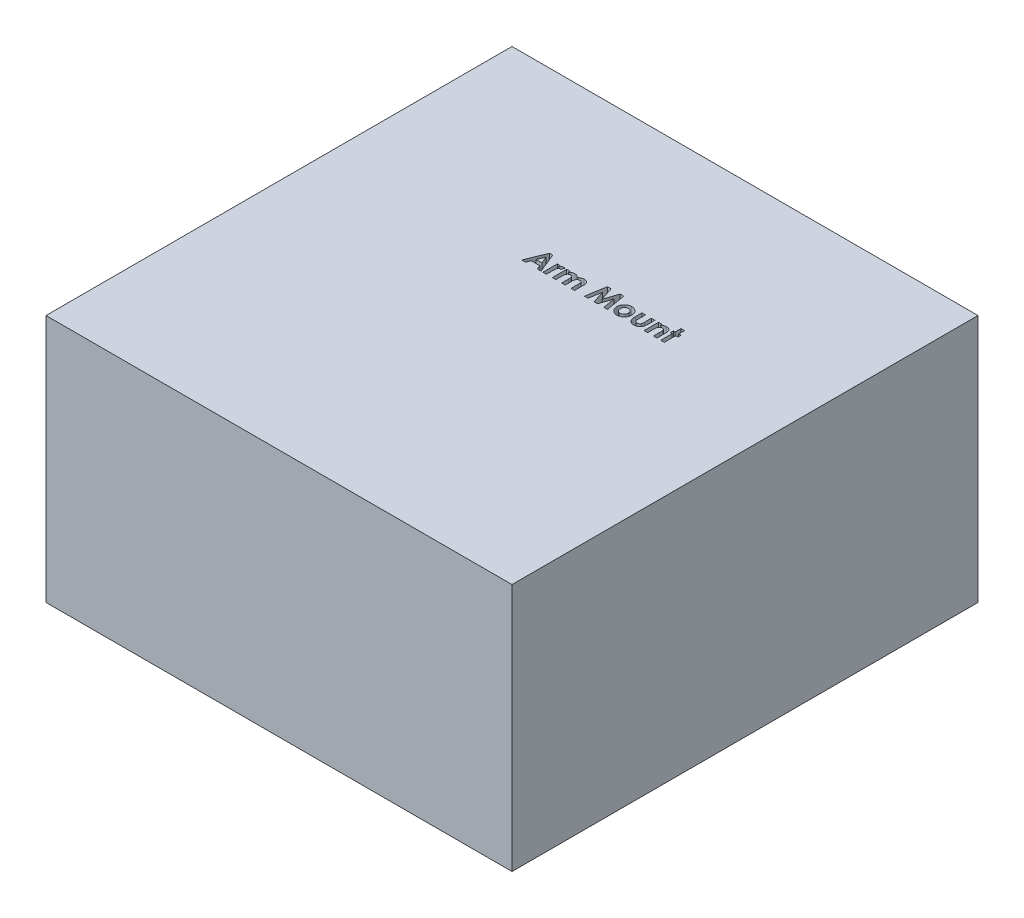
SolidWorks part; units mm, degrees
ref_plane "Front Plane" through (0, 0, 0) normal (0, 0, 1) x (1, 0, 0)
ref_plane "Top Plane" through (0, 0, 0) normal (0, 1, 0) x (1, 0, 0)
ref_plane "Right Plane" through (0, 0, 0) normal (1, 0, 0) x (0, 0, -1)
sketch "Sketch1" plane through (0, 0, 0) normal (0, 1, 0) x (1, 0, 0)
  line L1 (0, 0) -> (300, 0)
  line L2 (0, 0) -> (0, 300)
  line L3 (0, 300) -> (300, 300)
  line L4 (300, 0) -> (300, 300)
  dimension "D1" = 300
  dimension "D2" = 300
extrude "Boss-Extrude1" add sketch "Sketch1" along normal blind 160
sketch "Sketch2" plane through (0, 160, 0) normal (0, 1, 0) x (1, 0, 0)
  line L0 (121.9692, 184.0972) -> (291.4092, 184.0972) construction
  text T0 "<b>Arm Mount</b>" font "Century Gothic" height in points 48
extrude "Cut-Extrude1" cut sketch "Sketch2" against normal blind 160
